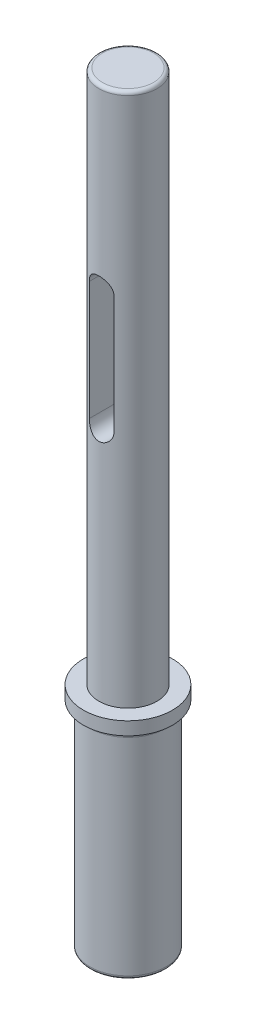
SolidWorks part; units mm, degrees
material "ABS Plastic"
ref_plane "Front Plane" through (0, 0, 0) normal (0, 0, 1) x (1, 0, 0)
ref_plane "Top Plane" through (0, 0, 0) normal (0, 1, 0) x (1, 0, 0)
ref_plane "Right Plane" through (0, 0, 0) normal (1, 0, 0) x (0, 0, -1)
sketch "Sketch1" plane through (0, 0, 0) normal (0, 1, 0) x (1, 0, 0)
  circle A0 centre (0, 0) radius 9.525
  dimension "D1" = 19.05
extrude "Boss-Extrude1" add sketch "Sketch1" along normal blind 163.322
sketch "Sketch2" plane through (0, 0, 0) normal (0, 1, 0) x (1, 0, 0)
  circle A0 centre (0, 0) radius 8.128
  dimension "D1" = 16.256
extrude "Cut-Extrude1" cut sketch "Sketch2" along normal blind 46.228 flip side to cut
ref_plane "Plane1" through (0, 163.322, 0) normal (0, 1, 0) x (1, 0, 0)
sketch "Sketch3" plane through (0, 163.322, 0) normal (0, 1, 0) x (1, 0, 0)
  circle A0 centre (0, 0) radius 6.223
  dimension "D1" = 12.446
extrude "Cut-Extrude2" cut sketch "Sketch3" against normal blind 114.3 flip side to cut
fillet "Fillet1" radius 1.27 1 edges at (0, 46.228, 8.128)
sketch "Sketch4" plane through (0, 0, 0) normal (0, 0, 1) x (1, 0, 0)
  line L0 (0, 125.222) -> (0, 99.822) construction
  line L1 (2.6353, 125.222) -> (2.6353, 99.822)
  line L2 (-2.6352, 125.222) -> (-2.6352, 99.822)
  line L3 (6.223, 163.322) -> (-6.223, 163.322) construction
  arc A0 (2.6353, 125.222) -> (-2.6352, 125.222) centre (0, 125.222) ccw
  arc A1 (-2.6352, 99.822) -> (2.6353, 99.822) centre (0, 99.822) ccw
  point P3 (0, 112.522)
  dimension "D1" = 38.1
  dimension "D3" = 5.2705
  dimension "D2" = 25.4
extrude "Cut-Extrude3" cut sketch "Sketch4" against normal through all both and the other way through all
fillet "Fillet2" radius 0.762 1 edges at (0, 163.322, 6.223)
fillet "Fillet3" radius 0.762 1 edges at (0, 0, 8.128)
